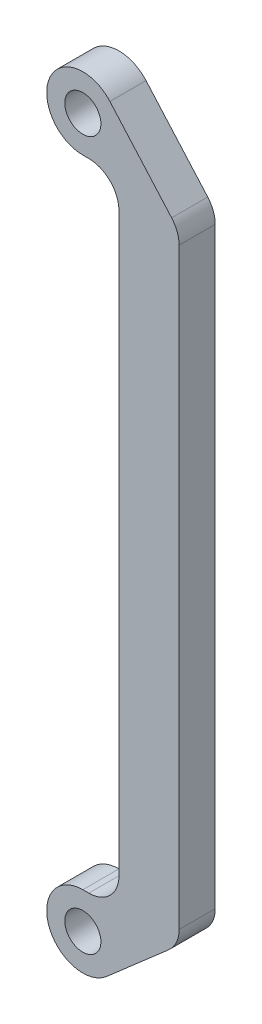
SolidWorks part; units mm, degrees
ref_plane "Alzado" through (0, 0, 0) normal (0, 0, 1) x (1, 0, 0)
ref_plane "Planta" through (0, 0, 0) normal (0, 1, 0) x (1, 0, 0)
ref_plane "Vista lateral" through (0, 0, 0) normal (1, 0, 0) x (0, 0, -1)
sketch "Croquis1" plane through (0, 0, 0) normal (0, 0, 1) x (1, 0, 0)
  line L0 (0, 0) -> (0, 117.69) construction
  line L2 (0, 123.69) -> (20.8772, 123.69) construction
  line L3 (0, -6) -> (20.8772, -6) construction
  line L4 (0, -6) -> (6, -6)
  line L5 (16, -6) -> (6, -6)
  line L6 (16, 8.2727) -> (16, 106.7273)
  line L7 (16, 123.69) -> (6, 123.69)
  line L8 (6, 11) -> (6, 106.69)
  line L9 (0, 6) -> (1, 6)
  line L10 (0, 123.69) -> (6, 123.69)
  line L11 (0, 111.69) -> (1, 111.69)
  line L12 (14.7502, 110.0342) -> (4.5003, 121.6583)
  line L13 (14.2877, 4.5056) -> (3.9452, -4.5205)
  arc A0 (-6, 0) -> (6, 0) centre (0, 0) ccw
  circle A1 centre (0, 0) radius 3
  circle A3 centre (0, 117.69) radius 3
  circle A5 centre (0, 0) radius 6
  circle A6 centre (0, 117.69) radius 6
  arc A7 (6, 106.69) -> (1, 111.69) centre (1, 106.69) ccw
  arc A8 (14.7502, 110.0342) -> (16, 106.7273) centre (11, 106.7273) cw
  arc A9 (16, 8.2727) -> (14.2877, 4.5056) centre (11, 8.2727) cw
  arc A10 (6, 11) -> (1, 6) centre (1, 11) cw
  dimension "D1" = 12
  dimension "D2" = 6
  dimension "D4" = 6
  dimension "D5" = 12
  dimension "D6" = 5
  dimension "D3" = 117.69
extrude "Saliente-Extruir1" add sketch "Croquis1" along normal blind 6 contours A0 A5 A1 | L8 A10 L9 A5 A0 L13 A9 L6 A8 L12 A6 L11 A7 | A6 A3
